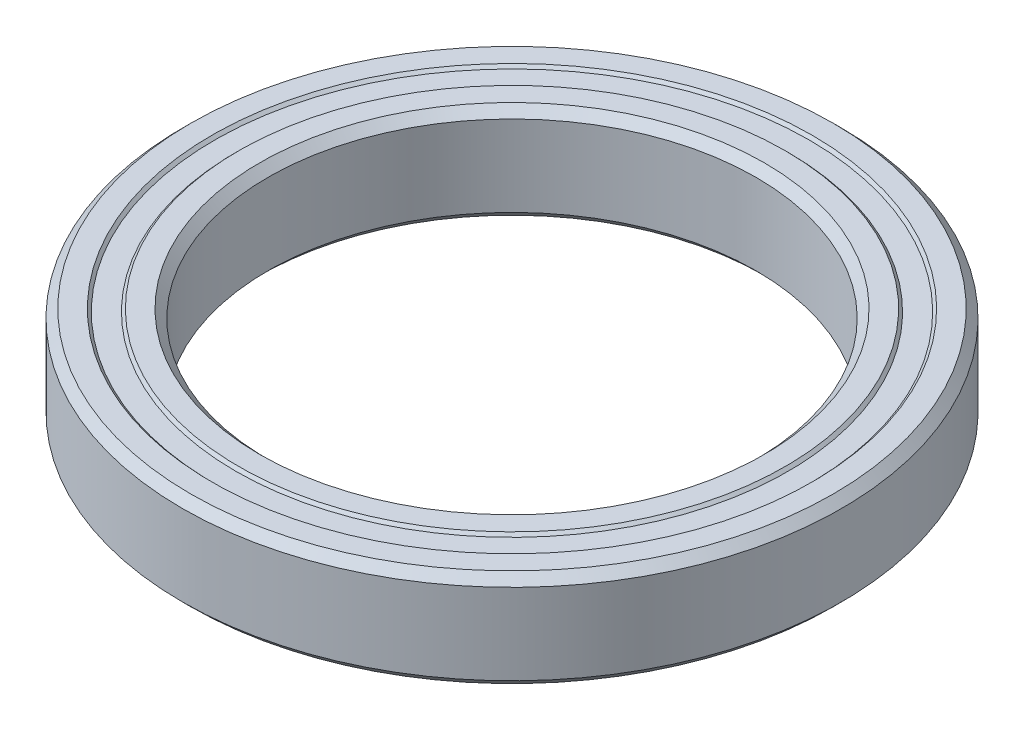
SolidWorks part; units mm, degrees
material "Stainless Steel (ferritic)"
ref_plane "Front Plane" through (0, 0, 0) normal (0, 0, 1) x (1, 0, 0)
ref_plane "Top Plane" through (0, 0, 0) normal (0, 1, 0) x (1, 0, 0)
ref_plane "Right Plane" through (0, 0, 0) normal (1, 0, 0) x (0, 0, -1)
sketch "Sketch1" plane through (0, 0, 0) normal (0, 0, 1) x (1, 0, 0)
  line L0 (0, -1.3494) -> (0, 70.5256) construction
  line L1 (10, 1.6572) -> (10, -1.6572)
  line L2 (10, -1.6572) -> (10.3428, -2)
  line L3 (10.3428, -2) -> (11.1999, -2)
  line L4 (11.1999, -2) -> (11.3142, -1.8857)
  line L5 (11.3142, -1.8857) -> (12.1858, -1.8857)
  line L6 (12.1858, -1.8857) -> (12.3001, -2)
  line L7 (12.3001, -2) -> (13.1572, -2)
  line L8 (13.1572, -2) -> (13.5, -1.6572)
  line L9 (13.5, -1.6572) -> (13.5, 1.6572)
  line L10 (13.5, 1.6572) -> (13.1572, 2)
  line L11 (13.1572, 2) -> (12.3001, 2)
  line L12 (12.3001, 2) -> (12.1858, 1.8857)
  line L13 (12.1858, 1.8857) -> (11.3142, 1.8857)
  line L14 (11.3142, 1.8857) -> (11.1999, 2)
  line L15 (11.1999, 2) -> (10.3428, 2)
  line L16 (10.3428, 2) -> (10, 1.6572)
  line L17 (0, 0) -> (10, 0) construction
  dimension "D1" = 10
  dimension "D2" = 4
  dimension "D3" = 0.3428
  dimension "D4" = 0.1143
  dimension "D5" = 13.5
  dimension "D6" = 0.8571
revolve "Revolve1" add sketch "Sketch1" angle 360 about L0
